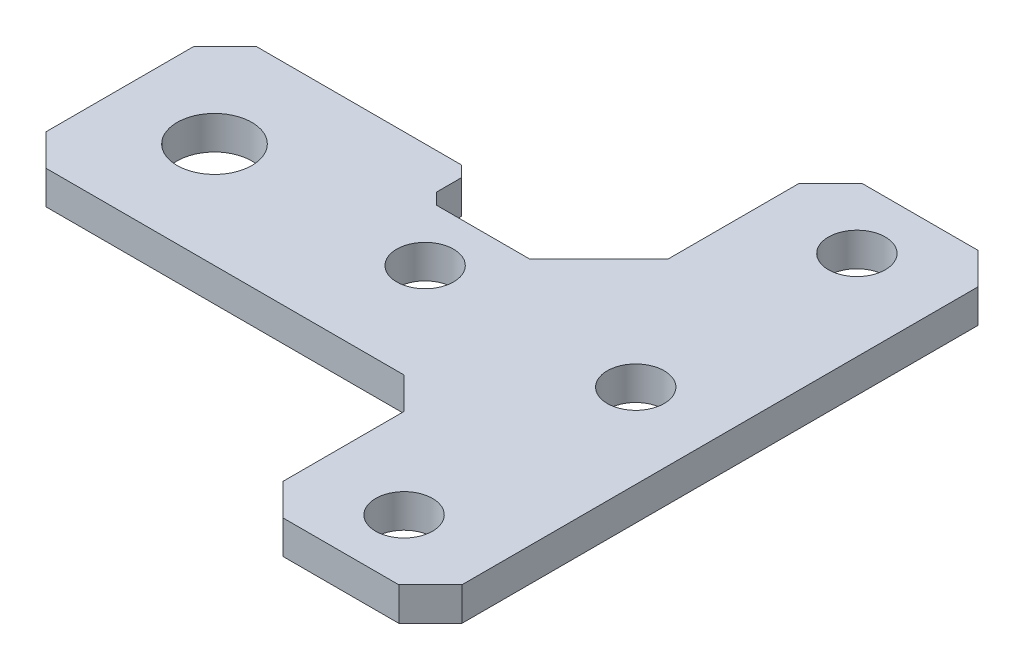
SolidWorks part; units mm, degrees
material "4032-T6"
ref_plane "Front Plane" through (0, 0, 0) normal (0, 0, 1) x (1, 0, 0)
ref_plane "Top Plane" through (0, 0, 0) normal (0, 1, 0) x (1, 0, 0)
ref_plane "Right Plane" through (0, 0, 0) normal (1, 0, 0) x (0, 0, -1)
sketch "Sketch1" plane through (0, 0, 0) normal (0, 1, 0) x (1, 0, 0)
  line L0 (57, 10) -> (0, 10) construction
  line L1 (0, 0) -> (40, 0)
  line L2 (0, 0) -> (0, 20)
  line L3 (0, 20) -> (40, 20)
  line L4 (48.5, 37.5) -> (48.5, -17.5) construction
  line L5 (40, -17.5) -> (57, -17.5)
  line L6 (40, -17.5) -> (40, 0)
  line L7 (40, 37.5) -> (57, 37.5)
  line L8 (57, -17.5) -> (57, 37.5)
  line L9 (40, 20) -> (40, 37.5)
  line L10 (19, 20) -> (19, 0) construction
  circle A0 centre (29, 10) radius 2.7
  circle A1 centre (9, 10) radius 3.55
  circle A2 centre (48.5, 31.5) radius 2.7
  circle A3 centre (48.5, -11.5) radius 2.7
  circle A4 centre (49, 10) radius 2.7
  dimension "D3" = 5.4
  dimension "D5" = 7.1
  dimension "D1" = 20
  dimension "D2" = 40
  dimension "D4" = 11
  dimension "D6" = 17
  dimension "D7" = 55
  dimension "D8" = 6
  dimension "D9" = 9
  dimension "D10" = 20
  dimension "D11" = 21
  dimension "D12" = 19.5
  dimension "D13" = 8.5
  dimension "D14" = 8.5
extrude "Boss-Extrude1" add sketch "Sketch1" along normal blind 3.175
chamfer "Chamfer1" distance 3 angle 45 6 edges at (57, 1.5875, 17.5) (40, 1.5875, 17.5) (0, 1.5875, 0) (57, 1.5875, -37.5) (40, 1.5875, -37.5) (0, 1.5875, -20)
sketch "Sketch3" plane through (0, 3.175, 0) normal (0, 1, 0) x (1, 0, 0)
  line L0 (21.8, 20) -> (21.8, 0) construction
  line L5 (21.8, 13) -> (21.8, 7) construction
  line L6 (23, 13) -> (23, 7)
  line L7 (20.6, 13) -> (20.6, 7)
  line L8 (16.8, 13) -> (16.8, 7) construction
  line L9 (3, 0) -> (40, 0) construction
  line L10 (0, 17) -> (0, 3) construction
  line L11 (40, 20) -> (3, 20) construction
  line L12 (18, 13) -> (18, 7)
  line L13 (15.6, 13) -> (15.6, 7)
  arc A0 (23, 13) -> (20.6, 13) centre (21.8, 13) ccw
  arc A1 (20.6, 7) -> (23, 7) centre (21.8, 7) ccw
  arc A2 (18, 13) -> (15.6, 13) centre (16.8, 13) ccw
  arc A3 (15.6, 7) -> (18, 7) centre (16.8, 7) ccw
  circle A4 centre (15.3, 17) radius 1.575
  circle A5 centre (15.3, 3) radius 1.575
  point P3 (21.8, 10)
  point P9 (21.8, 10)
  point P18 (16.8, 10)
  dimension "D2" = 1.2
  dimension "D5" = 1.2
  dimension "D9" = 3.15
  dimension "D1" = 21.8
  dimension "D3" = 6
  dimension "D4" = 5
  dimension "D6" = 6
  dimension "D7" = 1.5
  dimension "D8" = 7
  dimension "D10" = 14
sketch "Sketch6" plane through (0, 3.175, 0) normal (0, 1, 0) x (1, 0, 0)
  line L0 (23.5, 16.5607) -> (26.1607, 13.9)
  line L1 (26.1607, 13.9) -> (31.8393, 13.9)
  line L2 (31.8393, 13.9) -> (34.5, 16.5607)
  line L3 (34.5, 16.5607) -> (34.5, 18.2)
  line L4 (34.5, 18.2) -> (32.125, 18.2)
  line L5 (34.5, 18.2) -> (32.125, 18.2) construction
  line L6 (32.125, 18.2) -> (32.125, 18.545) construction
  line L7 (23.5, 16.5607) -> (23.5, 18.2)
  line L8 (23.5, 18.2) -> (25.875, 18.2)
  line L9 (25.875, 18.2) -> (25.875, 18.545)
  line L10 (25.875, 18.545) -> (24.42, 20)
  line L11 (40, 20) -> (3, 20) construction
  line L12 (24.42, 20) -> (25.875, 18.545) construction
  line L13 (32.125, 18.2) -> (32.125, 18.545)
  line L14 (32.125, 18.545) -> (33.58, 20)
  line L15 (32.125, 18.545) -> (33.58, 20) construction
  line L16 (33.58, 20) -> (24.42, 20)
extrude "Cut-Extrude2" cut sketch "Sketch6" against normal up to next
sketch "Sketch8" plane through (0, 0, 0) normal (0, -1, 0) x (1, 0, 0)
  line L0 (23.5, -18.2) -> (23.5, -20)
  line L1 (24.42, -20) -> (3, -20) construction
  line L2 (23.5, -20) -> (34.5, -20)
  line L3 (40, -20) -> (33.58, -20) construction
  line L4 (34.5, -20) -> (34.5, -18.2)
  line L5 (34.5, -18.2) -> (23.5, -18.2)
extrude "Cut-Extrude3" cut sketch "Sketch8" against normal up to next
sketch "Sketch9" plane through (0, 0, 0) normal (0, -1, 0) x (-1, 0, 0)
  line L0 (-24.5607, 15.5) -> (-33.4393, 15.5)
  line L1 (-23.5, 16.5607) -> (-26.1607, 13.9) construction
  line L2 (-31.8393, 13.9) -> (-34.5, 16.5607) construction
  line L3 (-23.5, 20) -> (-3, 20) construction
  line L4 (-24.5607, 15.5) -> (-24.5607, 13.9)
  line L5 (-24.5607, 13.9) -> (-33.4393, 13.9)
  line L6 (-33.4393, 13.9) -> (-33.4393, 15.5)
  line L7 (-26.1607, 13.9) -> (-31.8393, 13.9) construction
  dimension "D1" = 4.5
extrude "Boss-Extrude2" add sketch "Sketch9" against normal up to surface (3.175 mm away) up to face at (32.4, 3.175, -12.0461)
sketch "Sketch10" plane through (0, 0, 0) normal (0, -1, 0) x (1, 0, 0)
  line L0 (34.5, -16.5607) -> (40, -22.0607) construction
  line L1 (33.4393, -15.5) -> (34.5, -16.5607) construction
  line L2 (40, -22.0607) -> (40, -20)
  line L3 (37.9393, -20) -> (40, -22.0607)
  line L4 (40, -34.5) -> (40, -20) construction
  line L5 (40, -20) -> (37.9393, -20)
  line L6 (40, -20) -> (34.5, -20) construction
extrude "Boss-Extrude3" add sketch "Sketch10" against normal up to surface (3.175 mm away) up to face at (32.4, 3.175, -12.2061)
sketch "Sketch11" plane through (0, 0, 0) normal (0, -1, 0) x (1, 0, 0)
  line L0 (34.5, -16.5607) -> (37.9393, -20)
  line L1 (37.9393, -20) -> (34.5, -20)
  line L2 (34.5, -20) -> (34.5, -16.5607)
extrude "Cut-Extrude4" cut sketch "Sketch11" against normal up to next
chamfer "Chamfer3" distance 1.0607 angle 45 1 edges at (23.5, 1.5875, -20)
ref_plane "Plane1" through (0, 0, -10) normal (0, 0, -1) x (-1, 0, 0)
chamfer "Chamfer4" distance 3 angle 45 1 edges at (40, 1.5875, 0)
